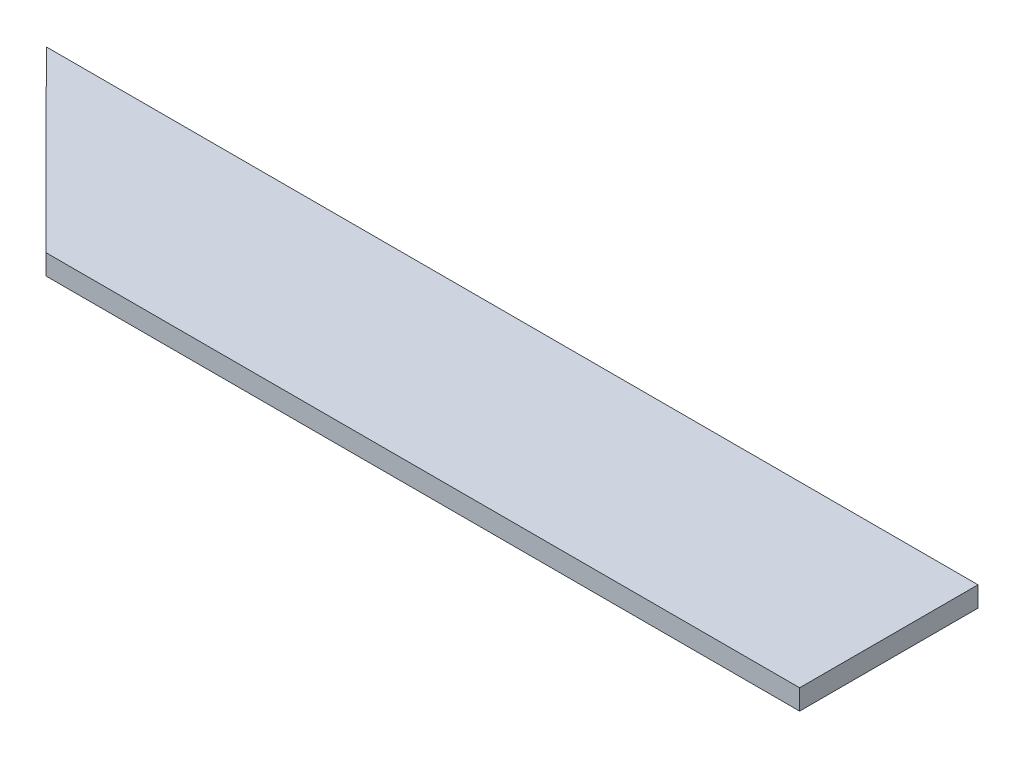
SolidWorks part; units mm, degrees
ref_plane "Front Plane" through (0, 0, 0) normal (0, 0, 1) x (1, 0, 0)
ref_plane "Top Plane" through (0, 0, 0) normal (0, 1, 0) x (1, 0, 0)
ref_plane "Right Plane" through (0, 0, 0) normal (1, 0, 0) x (0, 0, -1)
sketch "Sketch1" plane through (0, 0, 0) normal (0, 1, 0) x (1, 0, 0)
  line L0 (-99.1552, 31.9922) -> (-72.7798, 5.5709)
  line L1 (-99.1552, 31.9922) -> (38.8448, 31.9922)
  line L3 (-72.7798, 5.5709) -> (38.8448, 5.5709)
  line L4 (38.8448, 31.9922) -> (38.8448, 5.5709)
  point P2 (-99.1552, 31.9922)
  dimension "D1" = 138
extrude "Boss-Extrude1" add sketch "Sketch1" along normal blind 3
